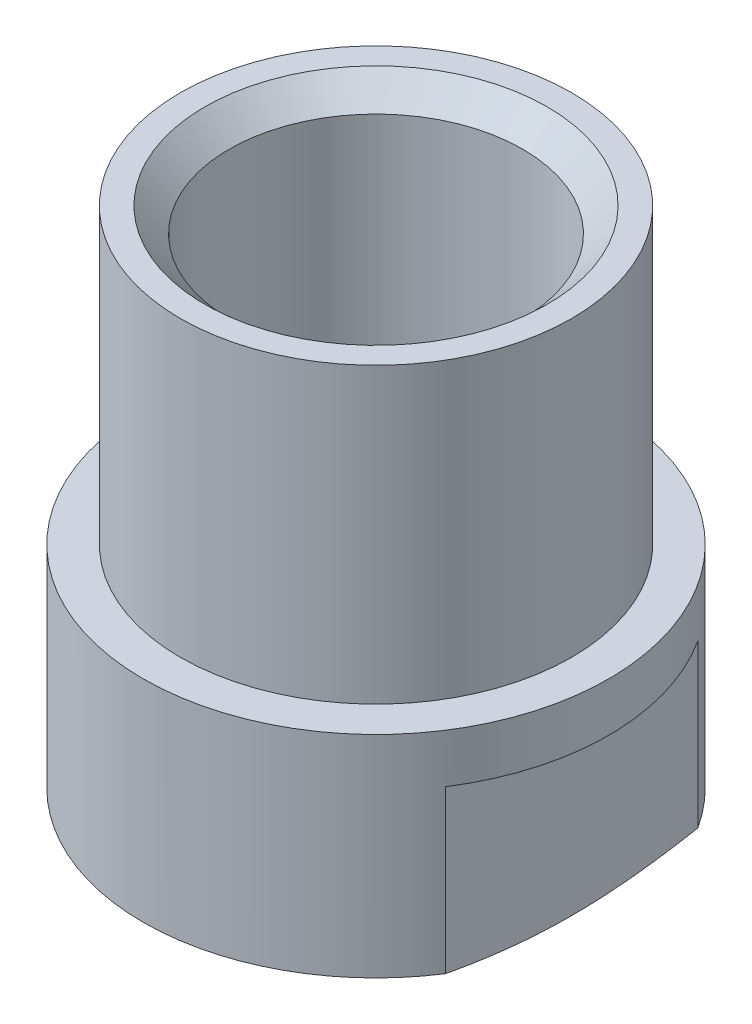
SolidWorks part; units mm, degrees
ref_plane "Alzado" through (0, 0, 0) normal (0, 0, 1) x (1, 0, 0)
ref_plane "Planta" through (0, 0, 0) normal (0, 1, 0) x (1, 0, 0)
ref_plane "Vista lateral" through (0, 0, 0) normal (1, 0, 0) x (0, 0, -1)
sketch "Croquis1" plane through (0, 0, 0) normal (0, 0, 1) x (1, 0, 0)
  line L0 (0, 26.2366) -> (0, -20) construction
  line L1 (2.3, 0) -> (4.76, 0)
  line L2 (4.76, 0) -> (4.76, 5)
  line L3 (4.76, 5) -> (4, 5)
  line L4 (4, 5) -> (4, 11)
  line L5 (4, 11) -> (3, 11)
  line L6 (3, 11) -> (3, 1)
  line L7 (3, 1) -> (1.5, 1)
  line L8 (1.5, 1) -> (1.5, 0.8)
  line L9 (1.5, 0.8) -> (2.3, 0)
  point P3 (1.5, 0)
  dimension "D1" = 5
  dimension "D2" = 6
  dimension "D3" = 1
  dimension "D4" = 4.76
  dimension "D5" = 4
  dimension "3" = 3
  dimension "D6" = 1.5
  dimension "D7" = 0.8
  dimension "D8" = 45
revolve "Revolución2" add sketch "Croquis1" angle 360 about L0
chamfer "Chaflán1" distance 2 angle 19 1 edges at (0, 0, 4.76)
chamfer "Chaflán2" distance 0.5 angle 45 1 edges at (0, 11, 3)
sketch "Croquis2" plane through (0, 0, 0) normal (0, -1, 0) x (1, 0, 0)
  line L1 (-4, -6) -> (4, -6)
  line L2 (-4, -6) -> (-4, 6)
  line L3 (-4, 6) -> (4, 6)
  line L4 (4, -6) -> (4, 6)
  line L5 (-4, -6) -> (4, 6) construction
  line L6 (-4, 6) -> (4, -6) construction
  point P0 (0, 0)
  dimension "D1" = 8
  dimension "D2" = 12
extrude "Cortar-Extruir1" cut sketch "Croquis2" against normal blind 4 flip side to cut
